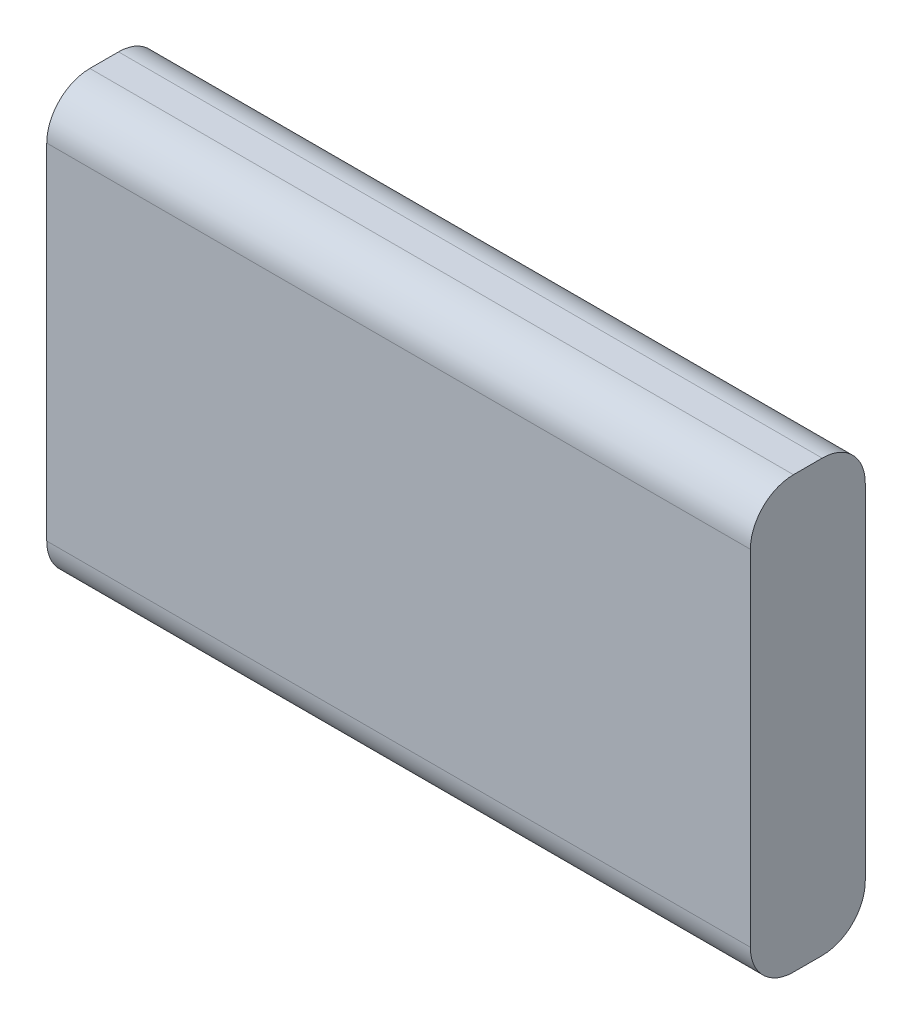
SolidWorks part; units mm, degrees
ref_plane "Front Plane" through (0, 0, 0) normal (0, 0, 1) x (1, 0, 0)
ref_plane "Top Plane" through (0, 0, 0) normal (0, 1, 0) x (1, 0, 0)
ref_plane "Right Plane" through (0, 0, 0) normal (1, 0, 0) x (0, 0, -1)
sketch "Sketch1" plane through (0, 0, 0) normal (0, 0, 1) x (1, 0, 0)
  line L1 (0, 0) -> (49, 0)
  line L2 (0, 0) -> (0, 30)
  line L3 (0, 30) -> (49, 30)
  line L4 (49, 0) -> (49, 30)
  dimension "D1" = 30
  dimension "D2" = 49
extrude "Boss-Extrude1" add sketch "Sketch1" along normal blind 8
fillet "Fillet1" radius 3 4 edges at (24.5, 0, 0) (24.5, 0, 8) (24.5, 30, 0) (24.5, 30, 8)
